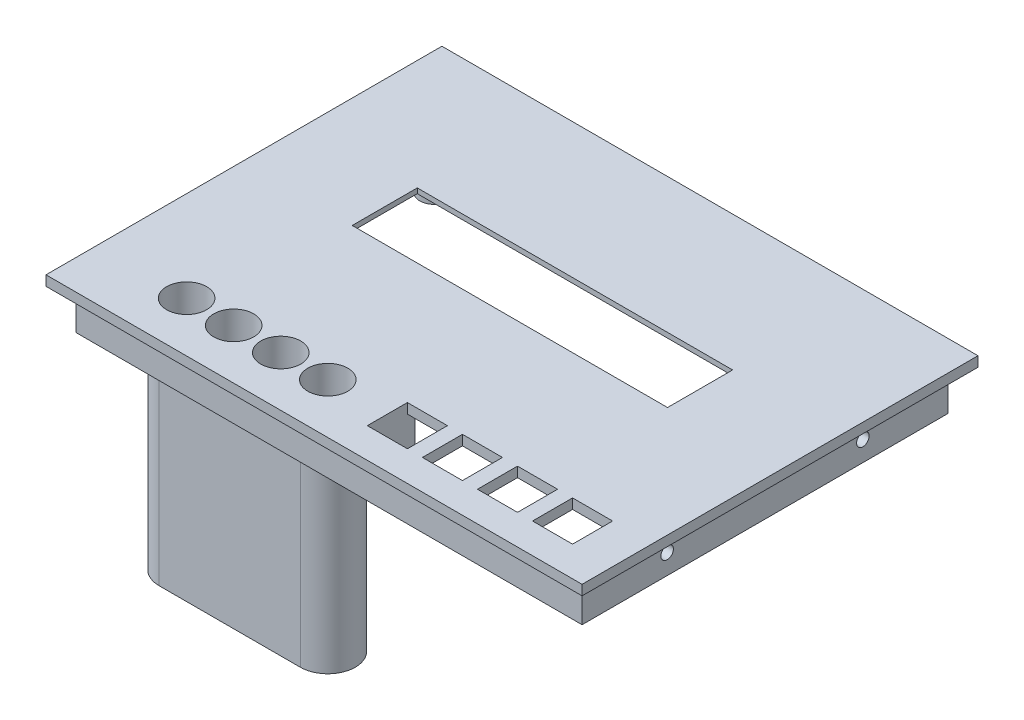
SolidWorks part; units mm, degrees
ref_plane "Front Plane" through (0, 0, 0) normal (0, 0, 1) x (1, 0, 0)
ref_plane "Top Plane" through (0, 0, 0) normal (0, 1, 0) x (1, 0, 0)
ref_plane "Right Plane" through (0, 0, 0) normal (1, 0, 0) x (0, 0, -1)
sketch "Sketch1" plane through (0, 0, 0) normal (0, 1, 0) x (1, 0, 0)
  line L1 (-39.05, -27.95) -> (39.05, -27.95)
  line L2 (-39.05, -27.95) -> (-39.05, 27.95)
  line L3 (-39.05, 27.95) -> (39.05, 27.95)
  line L4 (39.05, -27.95) -> (39.05, 27.95)
  line L5 (-39.05, -27.95) -> (39.05, 27.95) construction
  line L6 (-39.05, 27.95) -> (39.05, -27.95) construction
  point P0 (0, 0)
extrude "Boss-Extrude1" add sketch "Sketch1" along normal blind 3
sketch "Sketch2" plane through (0, 3, 0) normal (0, 1, 0) x (1, 0, 0)
  circle A0 centre (-35.9, 20.9) radius 1.25
  circle A1 centre (-35.9, -24.8) radius 1.25
  circle A2 centre (35.9, -24.8) radius 1.25
  circle A3 centre (35.9, 24.8) radius 1.25
extrude "Cut-Extrude1" cut sketch "Sketch2" against normal blind 68
sketch "Sketch3" plane through (0, 3, 0) normal (0, 1, 0) x (1, 0, 0)
  line L0 (-39.05, -27.95) -> (39.05, -27.95) construction
  line L5 (-31.15, -27.95) -> (8.45, -27.95)
  line L6 (-31.15, -27.95) -> (-31.15, -12.75)
  line L7 (-31.15, -12.75) -> (8.45, -12.75)
  line L8 (8.45, -27.95) -> (8.45, -12.75)
  line L13 (27.35, -17.65) -> (15.85, -17.65)
  line L14 (27.35, -17.65) -> (27.35, -27.95)
  line L15 (27.35, -27.95) -> (15.85, -27.95)
  line L16 (15.85, -17.65) -> (15.85, -27.95)
  line L18 (-39.05, 27.95) -> (39.05, 27.95)
  line L19 (-39.05, 27.95) -> (-39.05, -27.95)
  line L20 (-39.05, -27.95) -> (39.05, -27.95)
  line L21 (39.05, 27.95) -> (39.05, -27.95)
  line L22 (-31.15, -27.95) -> (-25.45, -27.95)
  line L23 (-31.15, -27.95) -> (-31.15, -20.45)
  line L24 (-31.15, -20.45) -> (-25.45, -20.45)
  line L25 (-25.45, -27.95) -> (-25.45, -20.45)
  line L26 (8.45, -27.95) -> (2.75, -27.95)
  line L27 (8.45, -27.95) -> (8.45, -20.45)
  line L28 (8.45, -20.45) -> (2.75, -20.45)
  line L29 (2.75, -27.95) -> (2.75, -20.45)
  line L30 (2.75, -27.95) -> (-6.65, -27.95)
  line L31 (2.75, -27.95) -> (2.75, -20.45)
  line L32 (2.75, -20.45) -> (-6.65, -20.45)
  line L33 (-6.65, -27.95) -> (-6.65, -20.45)
  line L34 (-25.45, -27.95) -> (-16.05, -27.95)
  line L35 (-25.45, -27.95) -> (-25.45, -20.45)
  line L36 (-25.45, -20.45) -> (-16.05, -20.45)
  line L37 (-16.05, -27.95) -> (-16.05, -20.45)
  circle A0 centre (35.9, 24.8) radius 1.25
  circle A1 centre (35.9, -24.8) radius 1.25
  circle A2 centre (-35.9, -24.8) radius 1.25
  circle A3 centre (-35.9, 20.9) radius 1.25
  circle A4 centre (2.75, -20.45) radius 4
  circle A5 centre (-6.65, -20.45) radius 4
  circle A6 centre (-16.05, -20.45) radius 4
  circle A7 centre (-25.45, -20.45) radius 4
sketch "Sketch4" plane through (0, 0, 0) normal (0, -1, 0) x (-1, 0, 0)
  line L0 (0, -27.95) -> (0, -29.95) construction
  line L1 (39.05, 27.95) -> (-39.05, 27.95)
  line L2 (39.05, 27.95) -> (39.05, -27.95)
  line L3 (39.05, -27.95) -> (-39.05, -27.95)
  line L4 (-39.05, 27.95) -> (-39.05, -27.95)
  line L5 (39.05, 27.95) -> (-39.05, -27.95) construction
  line L6 (39.05, -27.95) -> (-39.05, 27.95) construction
  line L7 (41.05, 29.95) -> (-41.05, 29.95)
  line L8 (41.05, 29.95) -> (41.05, -29.95)
  line L9 (41.05, -29.95) -> (-41.05, -29.95)
  line L10 (-41.05, 29.95) -> (-41.05, -29.95)
  line L11 (41.05, 29.95) -> (-41.05, -29.95) construction
  line L12 (41.05, -29.95) -> (-41.05, 29.95) construction
  line L13 (-39.05, 0) -> (-41.05, 0) construction
  point P0 (0, 0)
  point P7 (0, 0)
extrude "Boss-Extrude3" add sketch "Sketch4" against normal blind 3
sketch "Sketch6" plane through (0, 3, 0) normal (0, 1, 0) x (1, 0, 0)
  circle A0 centre (-35.9, -24.8) radius 1.25
  circle A1 centre (35.9, -24.8) radius 1.25
  circle A2 centre (35.9, 24.8) radius 1.25
  circle A3 centre (-35.9, 20.9) radius 1.25
  circle A4 centre (-35.9, 20.9) radius 3
  circle A5 centre (35.9, 24.8) radius 3
  circle A6 centre (35.9, -24.8) radius 3
  circle A7 centre (-35.9, -24.8) radius 3
extrude "Boss-Extrude4" add sketch "Sketch6" along normal blind 3.5
sketch "Sketch7" plane through (0, 0, 0) normal (0, -1, 0) x (-1, 0, 0)
  line L1 (-41.05, 29.95) -> (41.05, 29.95)
  line L2 (-41.05, 29.95) -> (-41.05, 46.15)
  line L3 (-41.05, 46.15) -> (41.05, 46.15)
  line L4 (41.05, 29.95) -> (41.05, 46.15)
extrude "Boss-Extrude5" add sketch "Sketch7" against normal blind 3
sketch "Sketch8" plane through (0, 0, -46.15) normal (0, 0, -1) x (-1, 0, 0)
  line L1 (-41.05, 0) -> (41.05, 0)
  line L2 (-41.05, 0) -> (-41.05, 50.5)
  line L3 (-41.05, 50.5) -> (41.05, 50.5)
  line L4 (41.05, 0) -> (41.05, 50.5)
extrude "Boss-Extrude6" add sketch "Sketch8" along normal blind 3
sketch "Sketch10" plane through (41.05, 0, 0) normal (1, 0, 0) x (0, 0, -1)
  line L1 (46.15, 50.5) -> (49.15, 50.5)
  line L2 (46.15, 50.5) -> (46.15, 0)
  line L3 (46.15, 0) -> (49.15, 0)
  line L4 (49.15, 50.5) -> (49.15, 0)
  line L5 (-29.95, 0) -> (46.15, 0)
  line L6 (-29.95, 0) -> (-29.95, 3)
  line L7 (-29.95, 3) -> (46.15, 3)
  line L8 (46.15, 0) -> (46.15, 3)
  line M1 (-29.95, 0) -> (49.15, 0)
  line M5 (46.15, 3) -> (-29.95, 3)
  line M6 (-29.95, 3) -> (-29.95, 0)
extrude "Boss-Extrude7" add sketch "Sketch10" along normal blind 20 contours L2 M5 M6 M1
sketch "Sketch12" plane through (-41.05, 0, 0) normal (-1, 0, 0) x (0, 0, 1)
  line L1 (-49.15, 50.5) -> (29.95, 50.5)
  line L2 (-49.15, 50.5) -> (-49.15, 0)
  line L3 (-49.15, 0) -> (29.95, 0)
  line L4 (29.95, 50.5) -> (29.95, 0)
extrude "Boss-Extrude8" add sketch "Sketch12" along normal blind 3
sketch "Sketch17" plane through (0, 0, 29.95) normal (0, 0, 1) x (1, 0, 0)
  line L1 (-44.05, 50.5) -> (61.05, 50.5)
  line L2 (-44.05, 50.5) -> (-44.05, 0)
  line L3 (-44.05, 0) -> (61.05, 0)
  line L4 (61.05, 50.5) -> (61.05, 0)
extrude "Boss-Extrude13" add sketch "Sketch17" against normal blind 2 and the other way blind 1
sketch "Sketch18" plane through (0, 0, 27.95) normal (0, 0, -1) x (-1, 0, 0)
  line L0 (-61.05, 3) -> (-61.05, 50.5) construction
  line L1 (41.05, 3) -> (-61.05, 3)
  line L2 (41.05, 3) -> (41.05, 6.5)
  line L4 (-61.05, 3) -> (-61.05, 6.5)
  line L10 (-8.45, 8.1) -> (-8.45, 13.1) construction
  line L19 (-8.45, 8.1) -> (-8.45, 22.1) construction
  line L21 (-8.45, 22.1) -> (31.15, 22.1)
  line L22 (-8.45, 22.1) -> (-8.45, 13.1)
  line L23 (-8.45, 13.1) -> (31.15, 13.1)
  line L24 (31.15, 22.1) -> (31.15, 13.1)
  line L31 (-25.35, 8.1) -> (-17.85, 11.8) construction
  line L32 (-25.35, 11.8) -> (-17.85, 8.1) construction
  line L38 (-27.35, 6.1) -> (-15.85, 6.1)
  line L39 (-27.35, 6.1) -> (-27.35, 13.8)
  line L40 (-27.35, 13.8) -> (-15.85, 13.8)
  line L41 (-15.85, 6.1) -> (-15.85, 13.8)
  line L42 (-27.35, 6.1) -> (-15.85, 13.8) construction
  line L43 (-27.35, 13.8) -> (-15.85, 6.1) construction
  point P7 (-21.6, 9.95)
  point P8 (-21.6, 9.95)
  point P27 (-21.6, 9.95)
  point P32 (-21.6, 9.95)
extrude "Cut-Extrude4" cut sketch "Sketch18" against normal blind 9 contours L38 L41 L40 L39 | L24 L21 L22 L23
sketch "Sketch19" plane through (61.05, 0, 0) normal (1, 0, 0) x (0, 0, -1)
  line L1 (-30.95, 50.5) -> (49.15, 50.5)
  line L2 (-30.95, 50.5) -> (-30.95, 0)
  line L3 (-30.95, 0) -> (49.15, 0)
  line L4 (49.15, 50.5) -> (49.15, 0)
extrude "Boss-Extrude14" add sketch "Sketch19" along normal blind 3
sketch "Sketch20" plane through (61.05, 0, 0) normal (-1, 0, 0) x (0, 0, 1)
  line L0 (-34.985, 3) -> (-34.985, 5) construction
  line L1 (-46.15, 3) -> (27.95, 3) construction
  line L2 (-46.15, 21.4946) -> (-44.15, 21.4946) construction
  line L3 (-46.15, 50.5) -> (-46.15, 3) construction
  line L4 (-44.15, 45) -> (-4.15, 5) construction
  line L14 (-39.9, 9.25) -> (-8.4, 40.75) construction
  line L15 (-39.9, 40.75) -> (-8.4, 9.25) construction
  circle A0 centre (-24.15, 25) radius 19
  circle A1 centre (-8.4, 40.75) radius 1.5
  circle A2 centre (-39.9, 40.75) radius 1.5
  circle A3 centre (-8.4, 9.25) radius 1.5
  circle A4 centre (-39.9, 9.25) radius 1.5
extrude "Cut-Extrude5" cut sketch "Sketch20" against normal blind 3
sketch "Sketch22" plane through (-41.05, 0, 0) normal (1, 0, 0) x (0, 0, -1)
  line L0 (46.15, 3) -> (27.95, 3) construction
  line L1 (-27.95, 3) -> (46.15, 3) construction
  line L2 (27.95, 3) -> (9.95, 3) construction
  line L3 (46.15, 26.75) -> (44.15, 26.75) construction
  line L4 (46.15, 3) -> (46.15, 50.5) construction
  line L5 (9.95, 45.5) -> (9.95, 36.125) construction
  line L6 (-27.95, 50.5) -> (46.15, 50.5) construction
  line L7 (44.15, 3) -> (44.15, 50.5) construction
  line L8 (18.5, 50.5) -> (18.5, 3) construction
  line L9 (9.95, 50.5) -> (18.5, 50.5) construction
  line L10 (27.05, 50.5) -> (27.05, 3) construction
  line L11 (18.5, 50.5) -> (27.05, 50.5) construction
  line L12 (35.6, 50.5) -> (35.6, 3) construction
  line L13 (27.05, 50.5) -> (35.6, 50.5) construction
  line L14 (35.6, 50.5) -> (44.15, 50.5) construction
  line L15 (14.225, 50.5) -> (14.225, 3) construction
  line L16 (22.775, 50.5) -> (22.775, 3) construction
  line L17 (31.325, 50.5) -> (31.325, 3) construction
  line L18 (39.875, 50.5) -> (39.875, 3) construction
  line L19 (9.95, 26.75) -> (44.15, 26.75) construction
  line L20 (9.95, 36.125) -> (9.95, 26.75) construction
  line L21 (9.95, 45.5) -> (44.15, 45.5) construction
  line L22 (9.95, 8) -> (44.15, 8) construction
  line L23 (9.95, 17.375) -> (44.15, 17.375) construction
  line L24 (9.95, 36.125) -> (44.15, 36.125) construction
  line L25 (9.95, 26.75) -> (9.95, 17.375) construction
  line L26 (9.95, 17.375) -> (9.95, 8) construction
  line L27 (9.95, 40.8125) -> (44.15, 40.8125) construction
  line L28 (9.95, 31.4375) -> (44.15, 31.4375) construction
  line L29 (9.95, 22.0625) -> (44.15, 22.0625) construction
  line L30 (9.95, 12.6875) -> (44.15, 12.6875) construction
  circle A0 centre (14.225, 12.6875) radius 2.5
  circle A1 centre (14.225, 22.0625) radius 2.5
  circle A2 centre (18.5, 17.375) radius 2.5
  circle A3 centre (22.775, 22.0625) radius 2.5
  circle A4 centre (22.775, 12.6875) radius 2.5
  circle A5 centre (14.225, 31.4375) radius 2.5
  circle A6 centre (18.5, 26.75) radius 2.5
  circle A7 centre (22.775, 31.4375) radius 2.5
  circle A8 centre (18.5, 36.125) radius 2.5
  circle A9 centre (14.225, 40.8125) radius 2.5
  circle A10 centre (22.775, 40.8125) radius 2.5
  circle A11 centre (27.05, 36.125) radius 2.5
  circle A12 centre (31.325, 40.8125) radius 2.5
  circle A13 centre (39.875, 40.8125) radius 2.5
  circle A14 centre (35.6, 36.125) radius 2.5
  circle A15 centre (39.875, 31.4375) radius 2.5
  circle A16 centre (31.325, 31.4375) radius 2.5
  circle A17 centre (27.05, 26.75) radius 2.5
  circle A18 centre (31.325, 22.0625) radius 2.5
  circle A19 centre (39.875, 22.0625) radius 2.5
  circle A20 centre (35.6, 26.75) radius 2.5
  circle A21 centre (27.05, 17.375) radius 2.5
  circle A22 centre (31.325, 12.6875) radius 2.5
  circle A23 centre (39.875, 12.6875) radius 2.5
  circle A24 centre (35.6, 17.375) radius 2.5
  circle A26 centre (18.5, 8) radius 2.5
  circle A27 centre (27.05, 8) radius 2.5
  circle A28 centre (35.6, 8) radius 2.5
extrude "Cut-Extrude6" cut sketch "Sketch22" against normal blind 3
sketch "Sketch23" plane through (64.05, 0, 0) normal (1, 0, 0) x (0, 0, -1)
  circle A0 centre (8.4, 9.25) radius 1.5
  circle A1 centre (39.9, 40.75) radius 1.5
extrude "Boss-Extrude16" add sketch "Sketch23" against normal blind 3
sketch "Sketch25" plane through (0, 0, 30.95) normal (0, 0, 1) x (1, 0, 0)
  line L1 (-44.05, 50.5) -> (64.05, 50.5)
  line L2 (-44.05, 50.5) -> (-44.05, 0)
  line L3 (-44.05, 0) -> (64.05, 0)
  line L4 (64.05, 50.5) -> (64.05, 0)
extrude "Cut-Extrude8" cut sketch "Sketch25" against normal blind 0.5
sketch "Sketch26" plane through (64.05, 0, 0) normal (1, 0, 0) x (0, 0, -1)
  line L1 (-30.45, 50.5) -> (49.15, 50.5)
  line L2 (-30.45, 50.5) -> (-30.45, 0)
  line L3 (-30.45, 0) -> (49.15, 0)
  line L4 (49.15, 50.5) -> (49.15, 0)
extrude "Cut-Extrude9" cut sketch "Sketch26" against normal blind 0.5
sketch "Sketch27" plane through (0, 0, -49.15) normal (0, 0, -1) x (-1, 0, 0)
  line L1 (-63.55, 50.5) -> (44.05, 50.5)
  line L2 (-63.55, 50.5) -> (-63.55, 0)
  line L3 (-63.55, 0) -> (44.05, 0)
  line L4 (44.05, 50.5) -> (44.05, 0)
extrude "Cut-Extrude10" cut sketch "Sketch27" against normal blind 0.5
sketch "Sketch28" plane through (-44.05, 0, 0) normal (-1, 0, 0) x (0, 0, 1)
  line L1 (-48.65, 50.5) -> (30.45, 50.5)
  line L2 (-48.65, 50.5) -> (-48.65, 0)
  line L3 (-48.65, 0) -> (30.45, 0)
  line L4 (30.45, 50.5) -> (30.45, 0)
extrude "Cut-Extrude11" cut sketch "Sketch28" against normal blind 0.5
sketch "Sketch30" plane through (0, 50.5, 0) normal (0, 1, 0) x (1, 0, 0)
  line L0 (61.05, 46.15) -> (-41.05, -27.95) construction
  line L1 (10, -27.45) -> (10, -27.95) construction
  line L2 (-40.55, 45.65) -> (60.55, 45.65)
  line L3 (-40.55, 45.65) -> (-40.55, -27.45)
  line L4 (-40.55, -27.45) -> (60.55, -27.45)
  line L5 (60.55, 45.65) -> (60.55, -27.45)
  line L6 (-40.55, 45.65) -> (60.55, -27.45) construction
  line L7 (-40.55, -27.45) -> (60.55, 45.65) construction
  line L8 (61.05, -27.95) -> (-41.05, -27.95) construction
  line L9 (60.55, 9.1) -> (61.05, 9.1) construction
  line L10 (61.05, 46.15) -> (61.05, -27.95) construction
  point P4 (10, 9.1)
extrude "Boss-Extrude17" add sketch "Sketch30" along normal blind 2 and the other way blind 6 separate body
sketch "Sketch31" plane through (0, 3, 0) normal (0, 1, 0) x (1, 0, 0)
  line L1 (-31.15, -12.75) -> (8.45, -12.75)
  line L2 (-31.15, -12.75) -> (-31.15, -27.95)
  line L3 (-31.15, -27.95) -> (8.45, -27.95)
  line L4 (8.45, -12.75) -> (8.45, -27.95)
extrude "Cut-Extrude12" cut sketch "Sketch31" against normal blind 18
sketch "Sketch32" plane through (0, 0, 0) normal (0, -1, 0) x (1, 0, 0)
  circle A0 centre (2.73, 16.5811) radius 4
  circle A1 centre (-6.6072, 16.5811) radius 4
  circle A2 centre (-16.03, 16.55) radius 4
  circle A3 centre (-25.43, 16.55) radius 4
extrude "Cut-Extrude13" cut sketch "Sketch32" against normal blind 788
sketch "Sketch35" plane through (0, 0, 30.45) normal (0, 0, 1) x (1, 0, 0)
  line L0 (10, 50.5) -> (10, 44.5) construction
  line L1 (63.55, 50.5) -> (-43.55, 50.5) construction
  line L2 (-43.55, 0) -> (-43.55, 50.5) construction
  line L3 (-43.55, 44.5) -> (84.6873, 44.5)
  line L4 (-43.55, 44.5) -> (-43.55, -56.9173)
  line L5 (-43.55, -56.9173) -> (84.6873, -56.9173)
  line L6 (84.6873, 44.5) -> (84.6873, -56.9173)
extrude "Cut-Extrude16" cut sketch "Sketch35" against normal blind 109
sketch "Sketch36" plane through (0, 50.5, 0) normal (0, 1, 0) x (1, 0, 0)
  line L1 (-43.55, 48.65) -> (63.55, 48.65)
  line L2 (-43.55, 48.65) -> (-43.55, -30.45)
  line L3 (-43.55, -30.45) -> (63.55, -30.45)
  line L4 (63.55, 48.65) -> (63.55, -30.45)
  line L5 (61.05, -27.95) -> (-41.05, -27.95)
  line L6 (61.05, -27.95) -> (61.05, 46.15)
  line L7 (61.05, 46.15) -> (-41.05, 46.15)
  line L8 (-41.05, -27.95) -> (-41.05, 46.15)
extrude "Boss-Extrude18" add sketch "Sketch36" along normal blind 2
sketch "Sketch37" plane through (0, 44.5, 0) normal (0, -1, 0) x (-1, 0, 0)
  line L1 (43.55, -30.45) -> (-63.55, -30.45)
  line L2 (43.55, -30.45) -> (43.55, 48.65)
  line L3 (43.55, 48.65) -> (-63.55, 48.65)
  line L4 (-63.55, -30.45) -> (-63.55, 48.65)
  line L5 (-61.05, 46.15) -> (41.05, 46.15)
  line L6 (-61.05, 46.15) -> (-61.05, -27.95)
  line L7 (-61.05, -27.95) -> (41.05, -27.95)
  line L8 (41.05, 46.15) -> (41.05, -27.95)
extrude "Cut-Extrude17" cut sketch "Sketch37" against normal blind 6
sketch "Sketch38" plane through (0, 52.5, 0) normal (0, 1, 0) x (1, 0, 0)
  line L1 (61.05, -27.95) -> (-41.05, -27.95)
  line L2 (61.05, -27.95) -> (61.05, 46.15)
  line L3 (61.05, 46.15) -> (-41.05, 46.15)
  line L4 (-41.05, -27.95) -> (-41.05, 46.15)
  line L5 (-32.3027, -6.1655) -> (10, -6.1655)
  line L6 (-32.3027, -6.1655) -> (-32.3027, -24.9297)
  line L7 (-32.3027, -24.9297) -> (10, -24.9297)
  line L8 (10, -6.1655) -> (10, -24.9297)
extrude "Boss-Extrude19" add sketch "Sketch38" against normal blind 2
sketch "Sketch39" plane through (0, 44.5, 0) normal (0, -1, 0) x (-1, 0, 0)
  line L0 (40.55, -27.45) -> (-60.55, 45.65) construction
  line L5 (-10, 45.65) -> (-10, 44.15) construction
  line L6 (-60.55, 9.1) -> (-59.05, 9.1) construction
  line L7 (-10, -27.45) -> (-10, -25.95) construction
  line L9 (39.05, 44.15) -> (-59.05, 44.15)
  line L10 (39.05, 44.15) -> (39.05, -25.95)
  line L11 (39.05, -25.95) -> (-59.05, -25.95)
  line L12 (-59.05, 44.15) -> (-59.05, -25.95)
  line L13 (39.05, 44.15) -> (-59.05, -25.95) construction
  line L14 (39.05, -25.95) -> (-59.05, 44.15) construction
  point P12 (-10, 9.1)
extrude "Cut-Extrude18" cut sketch "Sketch39" against normal blind 6
sketch "Sketch40" plane through (0, 50.5, 0) normal (0, -1, 0) x (-1, 0, 0)
  line L0 (25.43, -11.1817) -> (-2.73, -11.2439)
  line L1 (-2.73, -21.9183) -> (25.43, -21.9183)
  circle A0 centre (-2.73, -16.5811) radius 4
  circle A1 centre (6.6072, -16.5811) radius 4
  circle A3 centre (25.43, -16.55) radius 4
  circle A4 centre (-2.73, -16.5811) radius 5.3372
  circle A5 centre (25.43, -16.55) radius 5.3683
  circle A6 centre (16.03, -16.55) radius 4
  circle M4 centre (16.03, -16.55) radius 4
  circle M5 centre (-2.73, -16.5811) radius 4
  circle M10 centre (6.6072, -16.5811) radius 4
  circle M11 centre (25.43, -16.55) radius 4
extrude "Boss-Extrude21" add sketch "Sketch40" along normal blind 20 contours A5 L0 A4 L1 M10 M4 | A4 M5 | L0 A5 M11
sketch "Sketch43" plane through (59.05, 0, 0) normal (-1, 0, 0) x (0, 0, 1)
  line L5 (-0.65, 46) -> (-44.15, 46)
  line L6 (-0.65, 46) -> (-0.65, 44.5)
  line L7 (-0.65, 44.5) -> (-44.15, 44.5)
  line L8 (-44.15, 46) -> (-44.15, 44.5)
extrude "Cut-Extrude19" cut sketch "Sketch43" against normal blind 20
sketch "Sketch44" plane through (0, 0, -44.15) normal (0, 0, 1) x (1, 0, 0)
  line L0 (-39.05, 44.5) -> (60.55, 44.5) construction
  line L1 (60.55, 46) -> (38.55, 46)
  line L2 (60.55, 46) -> (60.55, 44.5)
  line L3 (60.55, 44.5) -> (38.55, 44.5)
  line L4 (38.55, 46) -> (38.55, 44.5)
extrude "Cut-Extrude20" cut sketch "Sketch44" against normal blind 20
fillet "Fillet1" radius 3 4 edges at (-30.7983, 50.5, 16.55) (-11.35, 50.5, 21.9183) (8.0672, 50.5, 16.5811) (-11.35, 50.5, 11.2128)
sketch "Sketch45" plane through (0, 50.5, 0) normal (0, -1, 0) x (-1, 0, 0)
  line L1 (39.05, -25.95) -> (-34.2088, -25.95)
  line L2 (39.05, -25.95) -> (39.05, 18.7182)
  line L3 (39.05, 18.7182) -> (-34.2088, 18.7182)
  line L4 (-34.2088, -25.95) -> (-34.2088, 18.7182)
extrude "Cut-Extrude21" cut sketch "Sketch45" along normal blind 63
extrude "Cut-Extrude22" cut sketch "Sketch3" against normal blind 374 and the other way blind 380 contours L36 A7 L24 | L24 A7 L35 | L35 A7 L36 | L36 A6 L37 | L37 A6 L36 | L32 A5 L33 | L33 A5 L32 | L32 A4 L31 | L31 A4 L28 | L28 A4 L32
sketch "Sketch49" plane through (0, 50.5, 0) normal (0, -1, 0) x (-1, 0, 0)
  circle A0 centre (25.45, -20.45) radius 4
  circle A1 centre (16.05, -20.45) radius 4
  circle A2 centre (6.65, -20.45) radius 4
  circle A3 centre (-2.75, -20.45) radius 4
  circle A4 centre (-2.73, -16.5811) radius 4
  circle A5 centre (6.6072, -16.5811) radius 4
  circle A6 centre (16.03, -16.55) radius 4
  circle A7 centre (25.43, -16.55) radius 4
  arc M3 (21.9476, -18.5179) -> (28.9324, -18.4821) centre (25.43, -16.55) cw
  arc M5 (12.5476, -18.5179) -> (19.5324, -18.4821) centre (16.03, -16.55) cw
  arc M7 (3.1277, -18.5543) -> (10.1294, -18.4768) centre (6.6072, -16.5811) cw
  arc M9 (-6.2411, -18.4974) -> (0.7611, -18.5336) centre (-2.73, -16.5811) cw
extrude "Boss-Extrude23" add sketch "Sketch49" against normal blind 2 contours A3 M9 | A2 M7 | A1 M5 | A0 M3
sketch "Sketch50" plane through (0, 50.5, 0) normal (0, -1, 0) x (-1, 0, 0)
  line L0 (25.45, -14.95) -> (-2.75, -14.95)
  line L1 (-2.75, -25.95) -> (25.45, -25.95)
  circle A0 centre (-2.75, -20.45) radius 5.5
  circle A1 centre (25.45, -20.45) radius 5.5
  circle M1 centre (25.45, -20.45) radius 4
  circle M2 centre (16.05, -20.45) radius 4
  circle M3 centre (6.65, -20.45) radius 4
  circle M4 centre (-2.75, -20.45) radius 4
  line M8 (-59.05, -25.95) -> (39.05, -25.95)
extrude "Boss-Extrude24" add sketch "Sketch50" along normal blind 23 contours A1 L0 A0 M3 M8 M2 | A1 M2 M1 | A0 M3 M4
fillet "Fillet2" radius 3 3 edges at (-30.95, 50.5, 20.45) (-11.35, 50.5, 14.95) (8.25, 50.5, 20.45)
sketch "Sketch51" plane through (0, 0, -45.65) normal (0, 0, -1) x (-1, 0, 0)
  line L0 (-60.55, 46) -> (-60.55, 50.5) construction
  line L1 (-38.55, 46) -> (-60.55, 46)
  line L2 (-38.55, 46) -> (-38.55, 46.5)
  line L3 (-38.55, 46.5) -> (-60.55, 46.5)
  line L4 (-60.55, 46) -> (-60.55, 46.5)
extrude "Cut-Extrude23" cut sketch "Sketch51" against normal blind 23
sketch "Sketch52" plane through (60.55, 0, 0) normal (1, 0, 0) x (0, 0, -1)
  line L1 (22.65, 46.5) -> (0.65, 46.5)
  line L2 (22.65, 46.5) -> (22.65, 46)
  line L3 (22.65, 46) -> (0.65, 46)
  line L4 (0.65, 46.5) -> (0.65, 46)
extrude "Cut-Extrude24" cut sketch "Sketch52" against normal blind 23
sketch "Sketch53" plane through (0, 52.5, 0) normal (0, 1, 0) x (1, 0, 0)
  line L0 (63.55, -24.45) -> (6.75, -24.45) construction
  line L1 (63.55, -30.45) -> (63.55, 48.65) construction
  line L2 (6.75, -24.45) -> (6.75, -20.45) construction
  line L3 (6.75, -20.45) -> (6.75, -16.45) construction
  line L4 (6.75, -16.45) -> (63.55, -16.45) construction
  line L5 (33.65, -20.45) -> (36.65, -20.45)
  line L6 (35.15, -24.45) -> (35.15, -16.45) construction
  line L7 (36.65, -20.45) -> (44.65, -20.45) construction
  line L8 (44.65, -20.45) -> (47.65, -20.45) construction
  line L9 (47.65, -20.45) -> (55.65, -20.45) construction
  line L10 (33.65, -20.45) -> (25.65, -20.45) construction
  line L11 (25.65, -20.45) -> (22.65, -20.45) construction
  line L12 (22.65, -20.45) -> (14.65, -20.45) construction
  line L14 (22.65, -24.45) -> (14.65, -24.45)
  line L15 (22.65, -24.45) -> (22.65, -16.45)
  line L16 (22.65, -16.45) -> (14.65, -16.45)
  line L17 (14.65, -24.45) -> (14.65, -16.45)
  line L18 (22.65, -24.45) -> (14.65, -16.45) construction
  line L19 (22.65, -16.45) -> (14.65, -24.45) construction
  line L20 (33.65, -24.45) -> (25.65, -24.45)
  line L21 (33.65, -24.45) -> (33.65, -16.45)
  line L22 (33.65, -16.45) -> (25.65, -16.45)
  line L23 (25.65, -24.45) -> (25.65, -16.45)
  line L24 (33.65, -24.45) -> (25.65, -16.45) construction
  line L25 (33.65, -16.45) -> (25.65, -24.45) construction
  line L26 (44.65, -24.45) -> (36.65, -24.45)
  line L27 (44.65, -24.45) -> (44.65, -16.45)
  line L28 (44.65, -16.45) -> (36.65, -16.45)
  line L29 (36.65, -24.45) -> (36.65, -16.45)
  line L30 (44.65, -24.45) -> (36.65, -16.45) construction
  line L31 (44.65, -16.45) -> (36.65, -24.45) construction
  line L32 (55.65, -24.45) -> (47.65, -24.45)
  line L33 (55.65, -24.45) -> (55.65, -16.45)
  line L34 (55.65, -16.45) -> (47.65, -16.45)
  line L35 (47.65, -24.45) -> (47.65, -16.45)
  line L36 (55.65, -24.45) -> (47.65, -16.45) construction
  line L37 (55.65, -16.45) -> (47.65, -24.45) construction
  circle A0 centre (2.75, -20.45) radius 4 construction
  point P10 (18.65, -20.45)
  point P14 (35.15, -20.45)
  point P25 (29.65, -20.45)
  point P30 (40.65, -20.45)
  point P35 (51.65, -20.45)
extrude "Cut-Extrude25" cut sketch "Sketch53" against normal blind 23 contours L35 L32 L33 L34 | L29 L26 L27 L28 | L23 L20 L21 L22 | L17 L14 L15 L16
sketch "Sketch54" plane through (0, 27.5, 0) normal (0, -1, 0) x (-1, 0, 0)
  line L0 (-2.75, -14.95) -> (25.45, -14.95)
  line L2 (35.5013, -14.95) -> (-14.2013, -14.95)
  line L3 (35.5013, -14.95) -> (35.5013, -25.95)
  line L4 (35.5013, -25.95) -> (-14.2013, -25.95)
  line L5 (-14.2013, -14.95) -> (-14.2013, -25.95)
  line L6 (35.5013, -14.95) -> (-14.2013, -25.95) construction
  line L7 (35.5013, -25.95) -> (-14.2013, -14.95) construction
  line L8 (35.5013, -14.95) -> (-14.2013, -14.95)
  line L9 (35.5013, -14.95) -> (35.5013, -4.0672)
  line L10 (35.5013, -4.0672) -> (-14.2013, -4.0672)
  line L11 (-14.2013, -14.95) -> (-14.2013, -4.0672)
  circle A0 centre (25.45, -20.45) radius 5.5
  circle A1 centre (-2.75, -20.45) radius 5.5
  circle A2 centre (6.65, -20.45) radius 4 construction
  point P10 (10.65, -20.45)
  line M3 (25.45, -14.95) -> (-2.75, -14.95)
  arc M4 (-2.75, -14.95) -> (-2.75, -25.95) centre (-2.75, -20.45) ccw
  arc M6 (25.45, -25.95) -> (25.45, -14.95) centre (25.45, -20.45) ccw
extrude "Cut-Extrude26" cut sketch "Sketch54" against normal blind 23 contours L11 L2 L9 L10 M3 | L4 L3 L2 M6 | L2 L5 L4 M4
sketch "Sketch56" plane through (0, 50.5, 0) normal (0, -1, 0) x (1, 0, 0)
  line L0 (59.05, -44.15) -> (59.05, 25.95) construction
  line L1 (55.65, 24.45) -> (59.05, 24.45)
  line L2 (55.65, 24.45) -> (55.65, 25.95)
  line L3 (55.65, 25.95) -> (59.05, 25.95)
  line L4 (59.05, 24.45) -> (59.05, 25.95)
  line L5 (55.65, 24.45) -> (59.05, 24.45)
  line L6 (55.65, 24.45) -> (55.65, 16.45)
  line L7 (55.65, 16.45) -> (59.05, 16.45)
  line L8 (59.05, 24.45) -> (59.05, 16.45)
  line L10 (59.05, 16.45) -> (55.65, 16.45)
  line L11 (59.05, 16.45) -> (59.05, 14.95)
  line L12 (59.05, 14.95) -> (55.65, 14.95)
  line L13 (55.65, 16.45) -> (55.65, 14.95)
  line M9 (59.05, 25.95) -> (2.75, 25.95)
  line M16 (59.05, -44.15) -> (59.05, 25.95)
  line M19 (55.65, 24.45) -> (55.65, 16.45)
extrude "Boss-Extrude25" add sketch "Sketch56" along normal blind 6 contours L2 L1 M16 M9 | L7 L1 M19 M16 | L7 L13 L12 M16
sketch "Sketch58" plane through (0, 50.5, 0) normal (0, -1, 0) x (1, 0, 0)
  line L0 (55.65, 25.95) -> (2.75, 25.95) construction
  line L1 (14.65, 25.95) -> (9.75, 25.95)
  line L2 (14.65, 25.95) -> (14.65, 14.95)
  line L3 (14.65, 14.95) -> (9.75, 14.95)
  line L4 (9.75, 25.95) -> (9.75, 14.95)
sketch "Sketch59" plane through (0, 44.5, 0) normal (0, -1, 0) x (-1, 0, 0)
extrude "Boss-Extrude26" add sketch "Sketch58" along normal blind 6
sketch "Sketch61" plane through (0, 44.5, 0) normal (0, -1, 0) x (-1, 0, 0)
  line L0 (-14.65, -25.95) -> (-9.75, -25.95) construction
  line L1 (-55.65, -25.95) -> (-60.55, -25.95) construction
  line L2 (-60.55, -27.45) -> (-60.55, 0.65) construction
  line L3 (-58.1, -25.95) -> (-58.1, -14.95) construction
  line L4 (-59.05, -14.95) -> (-55.65, -14.95) construction
  line L5 (-12.2, -25.95) -> (-12.2, -14.95) construction
  line L6 (-9.75, -14.95) -> (-14.65, -14.95) construction
  line L7 (-12.2, -20.45) -> (-58.1, -20.45) construction
  line L8 (-58.15, -20.45) -> (-12.15, -20.45)
  circle A0 centre (-58.15, -20.45) radius 1
  circle A1 centre (-12.15, -20.45) radius 1
  point P22 (-35.15, -20.45)
extrude "Cut-Extrude27" cut sketch "Sketch61" against normal blind 6
sketch "Sketch62" plane through (0, 44.5, 0) normal (0, -1, 0) x (-1, 0, 0)
  line L1 (-55.65, -14.95) -> (-59.05, -14.95)
  line L2 (-55.65, -14.95) -> (-55.65, 0.65)
  line L3 (-55.65, 0.65) -> (-59.05, 0.65)
  line L4 (-59.05, -14.95) -> (-59.05, 0.65)
extrude "Boss-Extrude27" add sketch "Sketch62" against normal blind 6
sketch "Sketch64" plane through (0, 44.5, 0) normal (0, -1, 0) x (1, 0, 0)
  line L1 (9.75, 14.95) -> (14.65, 14.95)
  line L2 (9.75, 14.95) -> (9.75, 25.95)
  line L3 (9.75, 25.95) -> (14.65, 25.95)
  line L4 (14.65, 14.95) -> (14.65, 25.95)
  line L5 (55.65, -0.65) -> (60.55, -0.65)
  line L6 (55.65, -0.65) -> (55.65, 27.45)
  line L7 (55.65, 27.45) -> (60.55, 27.45)
  line L8 (60.55, -0.65) -> (60.55, 27.45)
  line L9 (55.65, 25.95) -> (-40.55, 25.95)
  line L10 (55.65, 25.95) -> (55.65, 27.45)
  line L11 (55.65, 27.45) -> (-40.55, 27.45)
  line L12 (-40.55, 25.95) -> (-40.55, 27.45)
  line L13 (-40.55, 25.95) -> (-39.05, 25.95)
  line L14 (-40.55, 25.95) -> (-40.55, -44.15)
  line L15 (-40.55, -44.15) -> (-39.05, -44.15)
  line L16 (-39.05, 25.95) -> (-39.05, -44.15)
  line L17 (-40.55, -44.15) -> (38.55, -44.15)
  line L18 (-40.55, -44.15) -> (-40.55, -45.65)
  line L19 (-40.55, -45.65) -> (38.55, -45.65)
  line L20 (38.55, -44.15) -> (38.55, -45.65)
  circle M1 centre (58.15, 20.45) radius 1
  circle M2 centre (12.15, 20.45) radius 1
  line M3 (14.65, 25.95) -> (55.65, 25.95)
  line M4 (55.65, 25.95) -> (55.65, -0.65)
  line M5 (55.65, -0.65) -> (60.55, -0.65)
  line M6 (60.55, -0.65) -> (60.55, 27.45)
  line M7 (60.55, 27.45) -> (-40.55, 27.45)
  line M8 (-40.55, 27.45) -> (-40.55, -45.65)
  line M9 (-40.55, -45.65) -> (38.55, -45.65)
  line M10 (38.55, -45.65) -> (38.55, -44.15)
  line M11 (38.55, -44.15) -> (-39.05, -44.15)
  line M12 (-39.05, -44.15) -> (-39.05, 25.95)
  line M13 (-39.05, 25.95) -> (-25.45, 25.95)
  line M14 (-25.45, 25.95) -> (2.75, 25.95)
  line M15 (2.75, 25.95) -> (9.75, 25.95)
  line M16 (9.75, 25.95) -> (9.75, 14.95)
  line M17 (9.75, 14.95) -> (14.65, 14.95)
  line M18 (14.65, 14.95) -> (14.65, 25.95)
extrude "Boss-Extrude28" add sketch "Sketch64" along normal blind 2 contours L3 M16 M17 M18 M2 | L6 M4 M5 M6 M7 M1 | L9 L3 L6 M13 M14 M15 M3 M7 M8 | L15 L9 M8 M12 | L15 M8 M9 M10 M11
sketch "Sketch65" plane through (0, 50.5, 0) normal (0, -1, 0) x (-1, 0, 0)
  line L0 (-2.75, -14.95) -> (-9.75, -14.95)
  line L1 (-9.75, -14.95) -> (-9.75, -25.95)
  line L2 (-9.75, -25.95) -> (-2.75, -25.95)
  arc A0 (-2.75, -14.95) -> (-2.75, -25.95) centre (-2.75, -20.45) ccw construction
  circle A1 centre (-2.75, -20.45) radius 5.5
  line M22 (-9.75, -14.95) -> (-9.75, -25.95)
  line M23 (-9.75, -25.95) -> (-2.75, -25.95)
  arc M24 (-2.75, -25.95) -> (-2.75, -14.95) centre (-2.75, -20.45) cw
extrude "Boss-Extrude29" add sketch "Sketch65" along normal blind 8 contours L0 M24 M22 M23
sketch "Sketch67" plane through (0, 52.5, 0) normal (0, 1, 0) x (1, 0, 0)
  line L1 (63.55, -30.45) -> (-43.55, -30.45)
  line L2 (63.55, -30.45) -> (63.55, 48.65)
  line L3 (63.55, 48.65) -> (-43.55, 48.65)
  line L4 (-43.55, -30.45) -> (-43.55, 48.65)
  line L5 (55.65, -24.45) -> (47.65, -24.45)
  line L6 (55.65, -24.45) -> (55.65, -16.45)
  line L7 (55.65, -16.45) -> (47.65, -16.45)
  line L8 (47.65, -24.45) -> (47.65, -16.45)
  line L9 (44.65, -24.45) -> (36.65, -24.45)
  line L10 (44.65, -24.45) -> (44.65, -16.45)
  line L11 (44.65, -16.45) -> (36.65, -16.45)
  line L12 (36.65, -24.45) -> (36.65, -16.45)
  line L13 (33.65, -24.45) -> (25.65, -24.45)
  line L14 (33.65, -24.45) -> (33.65, -16.45)
  line L15 (33.65, -16.45) -> (25.65, -16.45)
  line L16 (25.65, -24.45) -> (25.65, -16.45)
  line L17 (22.65, -24.45) -> (14.65, -24.45)
  line L18 (22.65, -24.45) -> (22.65, -16.45)
  line L19 (22.65, -16.45) -> (14.65, -16.45)
  line L20 (14.65, -24.45) -> (14.65, -16.45)
  circle A0 centre (2.75, -20.45) radius 4
  circle A1 centre (-6.65, -20.45) radius 4
  circle A2 centre (-16.05, -20.45) radius 4
  circle A3 centre (-25.45, -20.45) radius 4
extrude "Boss-Extrude30" add sketch "Sketch67" along normal blind 22
sketch "Sketch68" plane through (0, 50.5, 0) normal (0, -1, 0) x (1, 0, 0)
  line L0 (-39.05, -44.15) -> (59.05, -44.15) construction
  line L1 (59.05, -44.15) -> (14.65, -44.15)
  line L2 (59.05, -44.15) -> (59.05, 16.45)
  line L3 (59.05, 16.45) -> (14.65, 16.45)
  line L4 (14.65, -44.15) -> (14.65, 16.45)
  line L5 (14.65, 14.95) -> (-39.05, 14.95)
  line L6 (14.65, 14.95) -> (14.65, -44.15)
  line L7 (14.65, -44.15) -> (-39.05, -44.15)
  line L8 (-39.05, 14.95) -> (-39.05, -44.15)
  line L9 (-25.45, 25.95) -> (-39.05, 25.95) construction
  line L10 (-39.05, -44.15) -> (-30.95, -44.15)
  line L11 (-39.05, -44.15) -> (-39.05, 25.95)
  line L12 (-39.05, 25.95) -> (-30.95, 25.95)
  line L13 (-30.95, -44.15) -> (-30.95, 25.95)
  circle A0 centre (-25.45, 20.45) radius 5.5
  line M4 (33.65, 16.45) -> (25.65, 16.45)
  line M8 (44.65, 16.45) -> (36.65, 16.45)
  line M9 (14.65, 16.45) -> (14.65, 14.95)
  line M10 (14.65, 14.95) -> (-25.45, 14.95)
  arc M11 (-25.45, 14.95) -> (-25.45, 25.95) centre (-25.45, 20.45) cw
  line M12 (-25.45, 25.95) -> (-39.05, 25.95)
  line M13 (-39.05, 25.95) -> (-39.05, -44.15)
  line M14 (-39.05, -44.15) -> (59.05, -44.15)
  line M15 (59.05, -44.15) -> (59.05, -0.65)
  line M16 (59.05, -0.65) -> (55.65, -0.65)
  line M17 (55.65, -0.65) -> (55.65, 16.45)
  line M18 (55.65, 16.45) -> (47.65, 16.45)
  line M26 (22.65, 16.45) -> (14.65, 16.45)
extrude "Cut-Extrude28" cut sketch "Sketch68" against normal blind 22 contours L4 L3 M14 M15 M16 M17 M18 M8 M4 M26 M9 | L13 L7 L4 L5 M10 | L13 L5 M14 M13 | L5 L13 M12 M13 | L13 L5 M11 | L13 M11 M12
sketch "Sketch70" plane through (0, 72.5, 0) normal (0, -1, 0) x (1, 0, 0)
  line L0 (59.05, -44.15) -> (-39.05, -44.15) construction
  line L1 (10, -15.6) -> (10, -44.15) construction
  line L8 (50, 2.4) -> (-30, -33.6) construction
  line L14 (47.5, -0.1) -> (-27.5, -31.1) construction
  line L15 (47.5, -31.1) -> (-27.5, -0.1) construction
  circle A0 centre (47.5, -31.1) radius 1.25
  circle A1 centre (-27.5, -31.1) radius 1.25
  circle A2 centre (-27.5, -0.1) radius 1.25
  circle A3 centre (47.5, -0.1) radius 1.25
  point P8 (10, -15.6)
  point P13 (10, -15.6)
extrude "Cut-Extrude29" cut sketch "Sketch70" against normal blind 22
sketch "Sketch71" plane through (0, 72.5, 0) normal (0, -1, 0) x (1, 0, 0)
  line L1 (10, -33.6) -> (10, -15.1748) construction
  line L2 (50, 2.4) -> (-30, 2.4)
  line L3 (50, 2.4) -> (50, -33.6)
  line L4 (50, -33.6) -> (-30, -33.6)
  line L5 (-30, 2.4) -> (-30, -33.6)
  line L10 (46.0987, -2.6748) -> (-26.0987, -27.6748) construction
  line L11 (46.0987, -27.6748) -> (-26.0987, -2.6748) construction
  line L12 (41.5, -8.6748) -> (-21.5, -8.6748)
  line L13 (41.5, -8.6748) -> (41.5, -21.6748)
  line L14 (41.5, -21.6748) -> (-21.5, -21.6748)
  line L15 (-21.5, -8.6748) -> (-21.5, -21.6748)
  line L16 (41.5, -8.6748) -> (-21.5, -21.6748) construction
  line L17 (41.5, -21.6748) -> (-21.5, -8.6748) construction
  point P4 (10, -15.6)
extrude "Cut-Extrude30" cut sketch "Sketch71" against normal blind 22 contours L13 L12 L15 L14
sketch "Sketch72" plane through (0, 72.5, 0) normal (0, -1, 0) x (-1, 0, 0)
  line L0 (-41.5, 8.6748) -> (21.5, 21.6748) construction
  line L2 (-46.1, 2.6748) -> (26.1, 2.6748)
  line L3 (-46.1, 2.6748) -> (-46.1, 27.6748)
  line L4 (-46.1, 27.6748) -> (26.1, 27.6748)
  line L5 (26.1, 2.6748) -> (26.1, 27.6748)
  line L6 (-46.1, 2.6748) -> (26.1, 27.6748) construction
  line L7 (-46.1, 27.6748) -> (26.1, 2.6748) construction
  point P4 (-10, 15.1748)
extrude "Cut-Extrude31" cut sketch "Sketch72" against normal blind 1
sketch "Sketch73" plane through (0, 72.5, 0) normal (0, -1, 0) x (-1, 0, 0)
  line L0 (-46.1, 27.6748) -> (26.1, 2.6748) construction
  line L2 (-46.1, 2.6748) -> (26.1, 2.6748)
  line L3 (-46.1, 2.6748) -> (-46.1, 27.6748)
  line L4 (-46.1, 27.6748) -> (26.1, 27.6748)
  line L5 (26.1, 2.6748) -> (26.1, 27.6748)
  line L6 (-46.1, 2.6748) -> (26.1, 27.6748) construction
  line L7 (-46.1, 27.6748) -> (26.1, 2.6748) construction
  line L8 (27.5, 28.9995) -> (-47.5, 28.9995)
  line L9 (27.5, 28.9995) -> (27.5, 1.35)
  line L10 (27.5, 1.35) -> (-47.5, 1.35)
  line L11 (-47.5, 28.9995) -> (-47.5, 1.35)
  line L12 (27.5, 28.9995) -> (-47.5, 1.35) construction
  line L13 (27.5, 1.35) -> (-47.5, 28.9995) construction
  circle A0 centre (-47.5, 0.1) radius 1.25 construction
  circle A1 centre (-47.5, 0.1) radius 2.9308
  circle A2 centre (27.5, 0.1) radius 2.9308
  circle A3 centre (27.5, 31.1) radius 2.93
  circle A4 centre (-47.5, 31.1) radius 2.93
  circle A5 centre (-47.5, 31.1) radius 1.25
  circle A6 centre (27.5, 31.1) radius 1.25
  circle A7 centre (27.5, 0.1) radius 1.25
  circle A8 centre (-47.5, 0.1) radius 1.25
  point P4 (-10, 15.1748)
  point P7 (-10, 15.1748)
  line M5 (26.1, 27.6748) -> (26.1, 2.6748)
  line M6 (26.1, 2.6748) -> (-46.1, 2.6748)
  line M7 (-46.1, 2.6748) -> (-46.1, 27.6748)
  line M8 (-46.1, 27.6748) -> (26.1, 27.6748)
  circle M9 centre (-47.5, 0.1) radius 1.25
  circle M10 centre (27.5, 0.1) radius 1.25
  circle M11 centre (27.5, 31.1) radius 1.25
  circle M12 centre (-47.5, 31.1) radius 1.25
extrude "Boss-Extrude31" add sketch "Sketch73" along normal blind 3 contours A4 L11 A1 A2 L9 A3 L8 M7 M8 M5 | L8 A4 L11 M12 | L11 A4 L8 | L10 A1 L11 | L11 A1 L10 M9 | A2 A1 L10 M6 | L9 A2 L10 | L10 A2 L9 M10 | L9 A3 L8 M11 | L8 A3 L9
sketch "Sketch74" plane through (0, 69.5, 0) normal (0, -1, 0) x (-1, 0, 0)
  circle A0 centre (-47.5, 31.1) radius 1.25
  circle A1 centre (-47.5, 31.1) radius 2.93
  circle A2 centre (-47.5, 0.1) radius 2.9308
  circle A3 centre (-47.5, 0.1) radius 1.25
  circle A4 centre (27.5, 0.1) radius 1.25
  circle A5 centre (27.5, 0.1) radius 2.9308
  circle A6 centre (27.5, 31.1) radius 1.25
  circle A7 centre (27.5, 31.1) radius 2.93
extrude "Boss-Extrude32" add sketch "Sketch74" along normal blind 3.5
sketch "Sketch75" plane through (0, 72.5, 0) normal (0, -1, 0) x (-1, 0, 0)
  line L1 (-55.65, -16.45) -> (-14.65, -16.45)
  line L2 (-55.65, -16.45) -> (-55.65, -14.95)
  line L3 (-55.65, -14.95) -> (-14.65, -14.95)
  line L4 (-14.65, -16.45) -> (-14.65, -14.95)
extrude "Boss-Extrude33" add sketch "Sketch75" along normal blind 22
sketch "Sketch76" plane through (0, 74.5, 0) normal (0, 1, 0) x (1, 0, 0)
  circle A0 centre (-27.5, 31.1) radius 1.25
  circle A1 centre (47.5, 31.1) radius 1.25
  circle A2 centre (47.5, 0.1) radius 1.25
  circle A3 centre (-27.5, 0.1) radius 1.25
extrude "Boss-Extrude34" add sketch "Sketch76" against normal blind 2
sketch "Sketch78" plane through (0, 50.5, 0) normal (0, -1, 0) x (-1, 0, 0)
  line L1 (-63.55, 48.65) -> (43.55, 48.65)
  line L2 (-63.55, 48.65) -> (-63.55, -30.45)
  line L3 (-63.55, -30.45) -> (43.55, -30.45)
  line L4 (43.55, 48.65) -> (43.55, -30.45)
  line L5 (40.55, -27.45) -> (-60.55, -27.45)
  line L6 (40.55, -27.45) -> (40.55, 45.65)
  line L7 (40.55, 45.65) -> (-60.55, 45.65)
  line L8 (-60.55, -27.45) -> (-60.55, 45.65)
extrude "Cut-Extrude32" cut sketch "Sketch78" against normal blind 22
sketch "Sketch79" plane through (0, 46.5, 0) normal (0, -1, 0) x (-1, 0, 0)
  line L1 (-38.55, 45.65) -> (-59.05, 45.65)
  line L2 (-38.55, 45.65) -> (-38.55, 44.15)
  line L3 (-38.55, 44.15) -> (-59.05, 44.15)
  line L4 (-59.05, 45.65) -> (-59.05, 44.15)
  line L5 (-60.55, 45.65) -> (-59.05, 45.65)
  line L6 (-60.55, 45.65) -> (-60.55, 0.65)
  line L7 (-60.55, 0.65) -> (-59.05, 0.65)
  line L8 (-59.05, 45.65) -> (-59.05, 0.65)
  line M1 (-59.05, 44.15) -> (-38.55, 44.15)
  line M2 (-38.55, 44.15) -> (-38.55, 45.65)
  line M3 (-38.55, 45.65) -> (-60.55, 45.65)
  line M4 (-60.55, 45.65) -> (-60.55, 0.65)
  line M5 (-60.55, 0.65) -> (-59.05, 0.65)
  line M6 (-59.05, 0.65) -> (-59.05, 44.15)
extrude "Cut-Extrude33" cut sketch "Sketch79" against normal blind 22 contours L4 M3 M4 M5 M6 | L4 M3 M1 M2
sketch "Sketch80" plane through (0, 42.5, 0) normal (0, -1, 0) x (-1, 0, 0)
  line L0 (-60.55, 0.65) -> (-60.55, -27.45) construction
  line L1 (-38.55, 45.65) -> (39.05, 45.65)
  line L2 (-38.55, 45.65) -> (-38.55, 44.15)
  line L3 (-38.55, 44.15) -> (39.05, 44.15)
  line L4 (39.05, 45.65) -> (39.05, 44.15)
  line L5 (40.55, 45.65) -> (39.05, 45.65)
  line L6 (40.55, 45.65) -> (40.55, -25.95)
  line L7 (40.55, -25.95) -> (39.05, -25.95)
  line L8 (39.05, 45.65) -> (39.05, -25.95)
  line L9 (40.55, -27.45) -> (-60.55, -27.45)
  line L10 (40.55, -27.45) -> (40.55, -25.95)
  line L11 (40.55, -25.95) -> (-60.55, -25.95)
  line L12 (-60.55, -27.45) -> (-60.55, -25.95)
  line L13 (-2.75, -14.95) -> (-14.65, -14.95)
  line L14 (-55.65, -25.95) -> (-60.55, -25.95)
  line L15 (-55.65, -25.95) -> (-55.65, 0.65)
  line L16 (-55.65, 0.65) -> (-60.55, 0.65)
  line L17 (-60.55, -25.95) -> (-60.55, 0.65)
  line L18 (-14.65, -14.95) -> (-14.65, -25.95)
  circle A0 centre (-2.75, -20.45) radius 5.5
  arc M1 (-2.75, -25.95) -> (-2.75, -14.95) centre (-2.75, -20.45) cw
  line M2 (-2.75, -14.95) -> (-14.65, -14.95)
  line M3 (-14.65, -14.95) -> (-14.65, -25.95)
  line M4 (-14.65, -25.95) -> (-55.65, -25.95)
  line M5 (-55.65, -25.95) -> (-55.65, 0.65)
  line M6 (-55.65, 0.65) -> (-60.55, 0.65)
  line M7 (-60.55, 0.65) -> (-60.55, -27.45)
  line M8 (-60.55, -27.45) -> (40.55, -27.45)
  line M9 (40.55, -27.45) -> (40.55, 45.65)
  line M10 (40.55, 45.65) -> (-38.55, 45.65)
  line M11 (-38.55, 45.65) -> (-38.55, 44.15)
  line M12 (-38.55, 44.15) -> (39.05, 44.15)
  line M13 (39.05, 44.15) -> (39.05, -25.95)
  line M14 (39.05, -25.95) -> (25.45, -25.95)
  line M15 (25.45, -25.95) -> (-2.75, -25.95)
  circle M16 centre (-12.15, -20.45) radius 1
  circle M17 centre (-58.15, -20.45) radius 1
extrude "Cut-Extrude34" cut sketch "Sketch80" against normal blind 22 contours L4 M10 M11 M12 | L7 L4 M9 M10 M13 | L11 L7 M15 M4 M7 M8 M9 M14 | L11 M1 M2 M3 M16 | L11 M5 M6 M7 M17
sketch "Sketch81" plane through (0, 50.5, 0) normal (0, -1, 0) x (-1, 0, 0)
  circle A0 centre (-58.15, -20.45) radius 1
  circle A1 centre (-12.15, -20.45) radius 1
extrude "Cut-Extrude35" cut sketch "Sketch81" against normal blind 22
sketch "Sketch82" plane through (0, 50.5, 0) normal (0, -1, 0) x (-1, 0, 0)
  line L1 (-55.65, -14.95) -> (-14.65, -14.95)
  line L2 (-55.65, -14.95) -> (-55.65, -25.95)
  line L3 (-55.65, -25.95) -> (-14.65, -25.95)
  line L4 (-14.65, -14.95) -> (-14.65, -25.95)
extrude "Cut-Extrude36" cut sketch "Sketch82" against normal blind 22
sketch "Sketch85" plane through (-43.55, 0, 0) normal (-1, 0, 0) x (0, 0, 1)
  circle A0 centre (-28.65, 68.5) radius 1.25
  circle A1 centre (10.45, 68.5) radius 1.25
extrude "Cut-Extrude38" cut sketch "Sketch85" against normal blind 9
sketch "Sketch86" plane through (63.55, 0, 0) normal (1, 0, 0) x (0, 0, -1)
  circle A0 centre (-10.3818, 68.6279) radius 1.25
extrude "Cut-Extrude39" cut sketch "Sketch86" against normal blind 9
sketch "Sketch88" plane through (0, 68.5, 0) normal (0, -1, 0) x (-1, 0, 0)
  line L1 (-38.55, 45.65) -> (-59.05, 45.65)
  line L2 (-38.55, 45.65) -> (-38.55, 44.15)
  line L3 (-38.55, 44.15) -> (-59.05, 44.15)
  line L4 (-59.05, 45.65) -> (-59.05, 44.15)
  line L5 (-60.55, 45.65) -> (-59.05, 45.65)
  line L6 (-60.55, 45.65) -> (-60.55, 0.65)
  line L7 (-60.55, 0.65) -> (-59.05, 0.65)
  line L8 (-59.05, 45.65) -> (-59.05, 0.65)
  line M1 (-59.05, 0.65) -> (-59.05, 44.15)
  line M2 (-59.05, 44.15) -> (-38.55, 44.15)
  line M3 (-38.55, 44.15) -> (-38.55, 45.65)
  line M4 (-38.55, 45.65) -> (-60.55, 45.65)
  line M5 (-60.55, 45.65) -> (-60.55, 0.65)
  line M6 (-60.55, 0.65) -> (-59.05, 0.65)
extrude "Boss-Extrude35" add sketch "Sketch88" along normal blind 4 contours L4 M4 M2 M3 | L4 M4 M5 M6 M1
sketch "Sketch89" plane through (0, 64.5, 0) normal (0, -1, 0) x (-1, 0, 0)
  line L0 (-60.55, 45.65) -> (-60.55, -27.45) construction
  line L1 (-55.65, 0.65) -> (-60.55, 0.65)
  line L2 (-55.65, 0.65) -> (-55.65, 45.65)
  line L3 (-55.65, 45.65) -> (-60.55, 45.65)
  line L4 (-60.55, 0.65) -> (-60.55, 45.65)
extrude "Boss-Extrude36" add sketch "Sketch89" against normal blind 9
sketch "Sketch90" plane through (0, 64.5, 0) normal (0, -1, 0) x (-1, 0, 0)
  line L0 (40.55, 45.65) -> (-60.55, 45.65) construction
  line L1 (40.55, -27.45) -> (35.65, -27.45)
  line L2 (40.55, -27.45) -> (40.55, 45.65)
  line L3 (40.55, 45.65) -> (35.65, 45.65)
  line L4 (35.65, -27.45) -> (35.65, 45.65)
extrude "Boss-Extrude37" add sketch "Sketch90" against normal blind 9
sketch "Sketch91" plane through (63.55, 0, 0) normal (1, 0, 0) x (0, 0, -1)
  circle A0 centre (28.65, 68.5) radius 1.25
extrude "Cut-Extrude41" cut sketch "Sketch91" against normal blind 9
sketch "Sketch92" plane through (60.55, 0, 0) normal (1, 0, 0) x (0, 0, -1)
  line L0 (45.65, 64.5) -> (-27.45, 64.5) construction
  line L1 (45.65, 72.5) -> (-15.7464, 72.5)
  line L2 (45.65, 72.5) -> (45.65, 64.5)
  line L3 (45.65, 64.5) -> (-15.7464, 64.5)
  line L4 (-15.7464, 72.5) -> (-15.7464, 64.5)
extrude "Boss-Extrude38" add sketch "Sketch92" against normal blind 4.9
sketch "Sketch94" plane through (63.55, 0, 0) normal (1, 0, 0) x (0, 0, -1)
  circle A0 centre (28.65, 68.5) radius 1.25
  circle A1 centre (-10.45, 68.5) radius 1.25
extrude "Cut-Extrude42" cut sketch "Sketch94" against normal blind 4.9
sketch "Sketch96" plane through (-43.55, 0, 0) normal (-1, 0, 0) x (0, 0, 1)
  circle A0 centre (10.45, 68.5) radius 1.25
  circle A1 centre (-28.65, 68.5) radius 1.25
extrude "Cut-Extrude43" cut sketch "Sketch96" against normal blind 9.9 contours A0 | A1
sketch "Sketch97" plane through (60.55, 0, 0) normal (1, 0, 0) x (0, 0, -1)
  circle A0 centre (28.65, 68.5) radius 1.25
  circle A1 centre (-10.45, 68.5) radius 1.25
extrude "Cut-Extrude44" cut sketch "Sketch97" against normal blind 9.9
